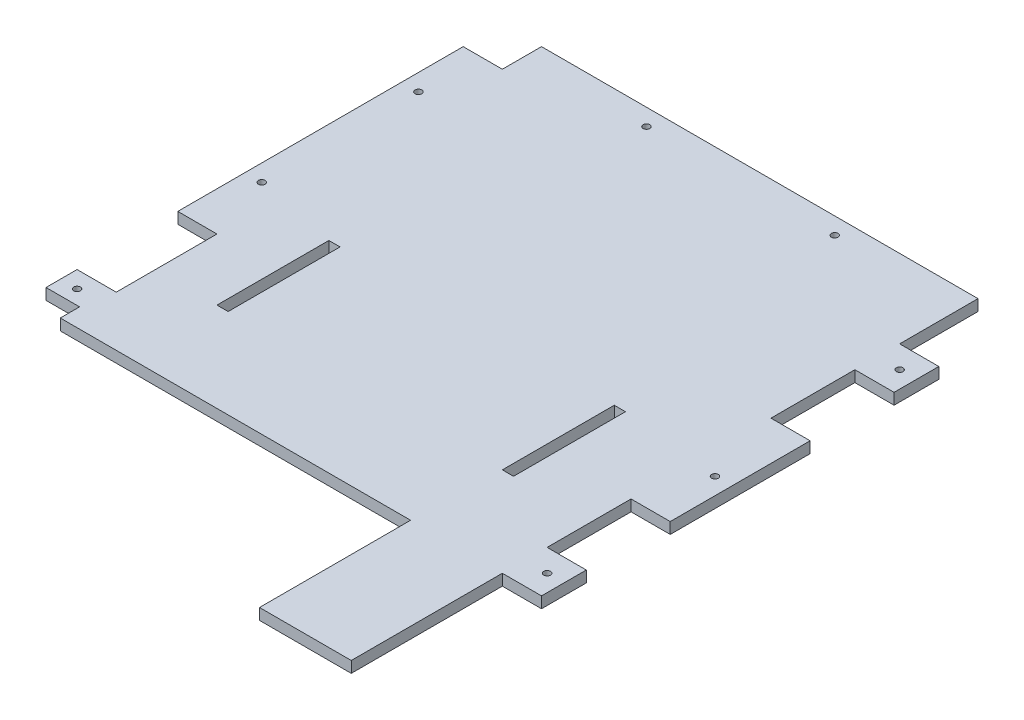
SolidWorks part; units mm, degrees
ref_plane "Front Plane" through (0, 0, 0) normal (0, 0, 1) x (1, 0, 0)
ref_plane "Top Plane" through (0, 0, 0) normal (0, 1, 0) x (1, 0, 0)
ref_plane "Right Plane" through (0, 0, 0) normal (1, 0, 0) x (0, 0, -1)
sketch "Sketch1" plane through (0, 0, 0) normal (0, 1, 0) x (1, 0, 0)
  line L0 (230, 560) -> (230, 0)
  line L1 (115, 315) -> (115, 215)
  line L2 (-230, 560) -> (-230, 152.2412)
  line L4 (113, 135) -> (113, 0)
  line L5 (-130, 315) -> (-130, 215)
  line L6 (-230, 152.2412) -> (-200, 152.2412)
  line L7 (-200, 152.2412) -> (-200, 135)
  line L8 (113, 135) -> (-200, 135)
  line L10 (-130, 215) -> (-140, 215)
  line L12 (-140, 215) -> (-140, 315)
  line L13 (-140, 315) -> (-130, 315)
  line L16 (115, 215) -> (125, 215)
  line L17 (125, 215) -> (125, 315)
  line L18 (125, 315) -> (115, 315)
  line L23 (-230, 560) -> (230, 560)
  line L32 (113, 0) -> (230, 0)
extrude "Boss-Extrude1" add sketch "Sketch1" along normal blind 10
sketch "Sketch2" plane through (0, 0, 0) normal (0, -1, 0) x (1, 0, 0)
  line L1 (230, -560) -> (195, -560)
  line L2 (230, -560) -> (230, -490)
  line L3 (230, -490) -> (195, -490)
  line L4 (195, -560) -> (195, -490)
  line L5 (-230, -560) -> (-195, -560)
  line L6 (-230, -560) -> (-230, -525)
  line L7 (-230, -525) -> (-195, -525)
  line L8 (-195, -560) -> (-195, -525)
  line L9 (-195, -180) -> (-230, -180)
  line L10 (-195, -180) -> (-195, -270)
  line L11 (-195, -270) -> (-230, -270)
  line L12 (-230, -180) -> (-230, -270)
  line L13 (230, -134.9836) -> (195, -134.9836)
  line L14 (230, -134.9836) -> (230, 0)
  line L15 (230, 0) -> (195, 0)
  line L16 (195, -134.9836) -> (195, 0)
  line L17 (230, -250) -> (195, -250)
  line L18 (230, -250) -> (230, -175)
  line L19 (230, -175) -> (195, -175)
  line L20 (195, -250) -> (195, -175)
  line L21 (230, -450) -> (195, -450)
  line L22 (230, -450) -> (230, -375)
  line L23 (230, -375) -> (195, -375)
  line L24 (195, -450) -> (195, -375)
  circle A0 centre (215, -470) radius 3
  circle A1 centre (215, -155) radius 3
  circle A2 centre (215, -305) radius 3
  circle A3 centre (-215, -165) radius 3
  circle A5 centre (-215, -470) radius 3
  circle A6 centre (-215, -330) radius 3
  circle A7 centre (81.9662, -545) radius 3
  circle A8 centre (-86.234, -545) radius 3
extrude "Cut-Extrude1" cut sketch "Sketch2" against normal blind 10
